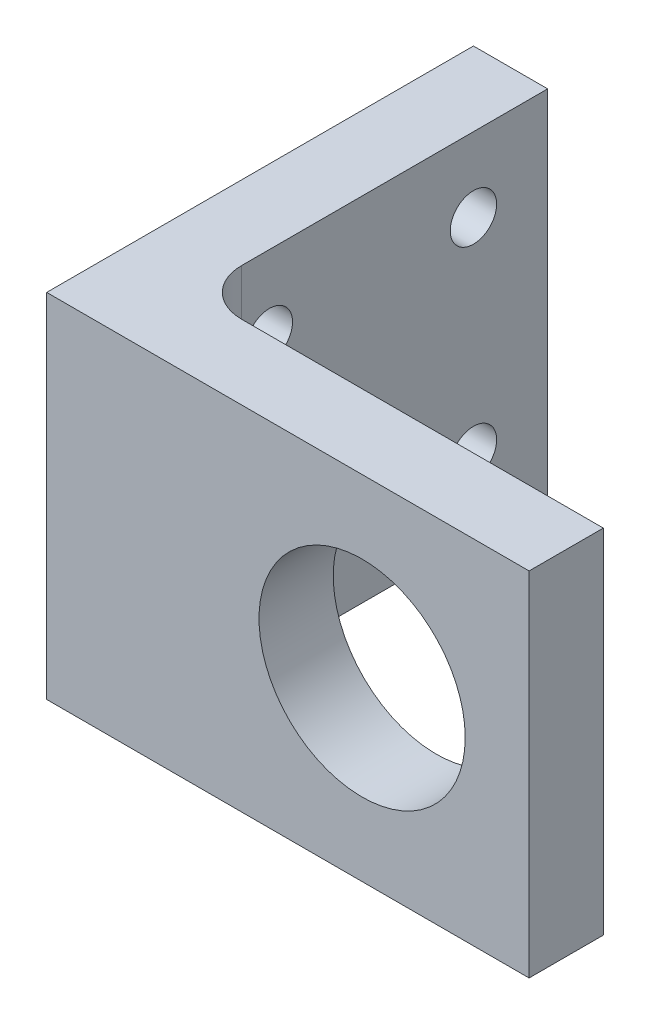
SolidWorks part; units mm, degrees
ref_plane "Piano frontale" through (0, 0, 0) normal (0, 0, 1) x (1, 0, 0)
ref_plane "Piano superiore" through (0, 0, 0) normal (0, 1, 0) x (1, 0, 0)
ref_plane "Piano destro" through (0, 0, 0) normal (1, 0, 0) x (0, 0, -1)
sketch "Sketch1" plane through (0, 0, 0) normal (0, 0, 1) x (1, 0, 0)
  line L0 (0, 19) -> (52, 19) construction
  line L1 (0, 0) -> (52, 0)
  line L2 (0, 0) -> (0, 38)
  line L3 (0, 38) -> (52, 38)
  line L4 (52, 0) -> (52, 38)
  circle A0 centre (34, 19) radius 11.1125
  dimension "D2" = 22.225
  dimension "D1" = 52
  dimension "D3" = 18
  dimension "D8" = 38
extrude "FaceUp" add sketch "Sketch1" along normal blind 8
sketch "Sketch8" plane through (0, 0, 0) normal (0, 0, -1) x (-1, 0, 0)
  line L0 (-52, 38) -> (0, 38) construction
  line L6 (0, 38) -> (0, 0) construction
  line L7 (-16.35, 19) -> (-34, 19) construction
  line L11 (-18.1947, 25) -> (-18.1947, 24.9954)
  line L12 (0, 0) -> (-52, 0) construction
  line L17 (0, 38) -> (-8, 38)
  line L18 (0, 38) -> (0, 0)
  line L19 (0, 0) -> (-8, 0)
  line L20 (-8, 38) -> (-8, 0)
  dimension "D1" = 8
extrude "FaceDown" add sketch "Sketch8" along normal blind 38
fillet "Fillet1" radius 5 1 edges at (8, 19, 0)
sketch "Sketch9" plane through (0, 0, 0) normal (-1, 0, 0) x (0, 0, 1)
  line L0 (0, 38) -> (0, 0) construction
  line L1 (8, 38) -> (-38, 38) construction
  line L2 (8, 38) -> (8, 0) construction
  line L3 (-38, 19) -> (8, 19) construction
  line L4 (-38, 0) -> (-38, 38) construction
  line L5 (-38, 0) -> (0, 38) construction
  line L7 (-38, 38) -> (0, 0) construction
  line L8 (-19, 19) -> (-19, 38) construction
  line L9 (-19, 38) -> (-19, 0) construction
  line L10 (8, 0) -> (-38, 0) construction
  circle A0 centre (-8, 30) radius 2.5
  circle A1 centre (-30, 30) radius 2.5
  circle A2 centre (-8, 8) radius 2.5
  circle A3 centre (-30, 8) radius 2.5
  dimension "D2" = 5
  dimension "D1" = 8
  dimension "D3" = 8
extrude "ScrewHoles" cut sketch "Sketch9" against normal blind 8
